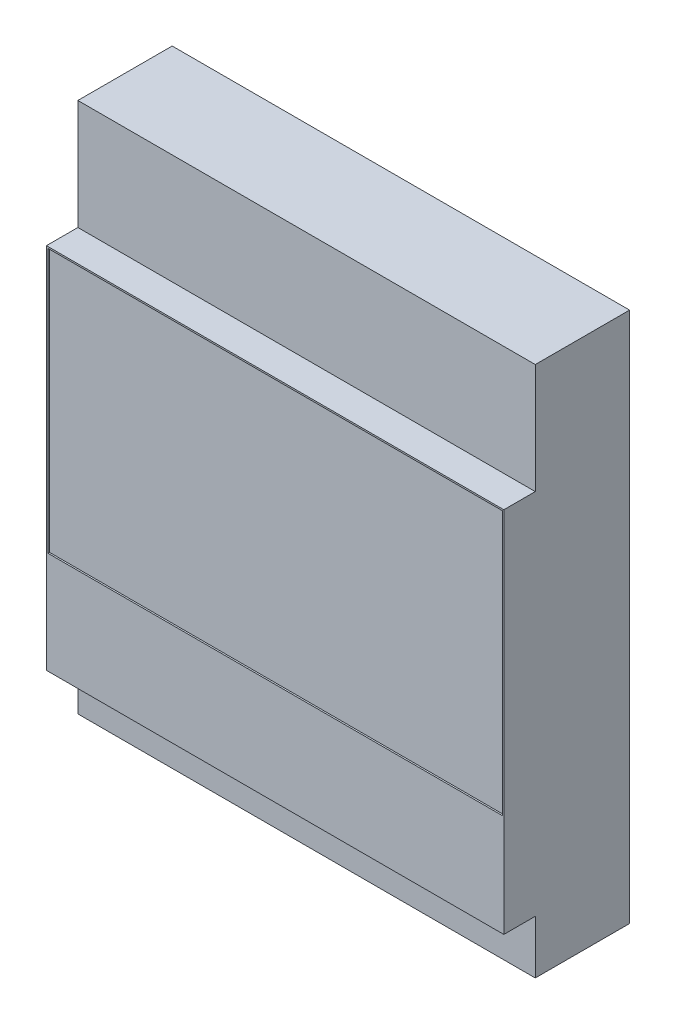
SolidWorks part; units mm, degrees
ref_plane "Спереди" through (0, 0, 0) normal (0, 0, 1) x (1, 0, 0)
ref_plane "Сверху" through (0, 0, 0) normal (0, 1, 0) x (1, 0, 0)
ref_plane "Справа" through (0, 0, 0) normal (1, 0, 0) x (0, 0, -1)
sketch "Эскиз1" plane through (0, 0, 0) normal (0, 0, 1) x (1, 0, 0)
  line L1 (-7.275, -5.85) -> (7.275, -5.85)
  line L2 (-7.275, -5.85) -> (-7.275, 5.85)
  line L3 (-7.275, 5.85) -> (7.275, 5.85)
  line L4 (7.275, -5.85) -> (7.275, 5.85)
  line L5 (-7.275, -5.85) -> (7.275, 5.85) construction
  line L6 (-7.275, 5.85) -> (7.275, -5.85) construction
  point P0 (0, 0)
  dimension "D1" = 14.55
  dimension "D2" = 11.7
extrude "Бобышка-Вытянуть1" add sketch "Эскиз1" along normal blind 1
sketch "Эскиз2" plane through (0, 0, 1) normal (0, 0, 1) x (1, 0, 0)
  line L0 (7.275, 5.85) -> (-7.275, 5.85) construction
  line L1 (-7.225, 5.8) -> (7.225, 5.8)
  line L2 (-7.225, 5.8) -> (-7.225, -2.6)
  line L3 (-7.225, -2.6) -> (7.225, -2.6)
  line L4 (7.225, 5.8) -> (7.225, -2.6)
  line L5 (7.275, -5.85) -> (7.275, 5.85) construction
  line L6 (-7.275, 5.85) -> (-7.275, -5.85) construction
  dimension "D1" = 0.05
  dimension "D2" = 0.05
  dimension "D3" = 0.05
  dimension "D4" = 8.45
extrude "Вырез-Вытянуть1" cut sketch "Эскиз2" against normal blind 0.05
sketch "Эскиз3" plane through (0, 0, 0) normal (0, 0, -1) x (-1, 0, 0)
  line L0 (7.275, 5.85) -> (7.275, -5.85) construction
  line L1 (-7.275, 9.35) -> (7.275, 9.35)
  line L2 (-7.275, 9.35) -> (-7.275, -7.55)
  line L3 (-7.275, -7.55) -> (7.275, -7.55)
  line L4 (7.275, 9.35) -> (7.275, -7.55)
  line L5 (-7.275, -5.85) -> (-7.275, 5.85) construction
  line L6 (7.275, -5.85) -> (-7.275, -5.85) construction
  line L7 (-7.275, 5.85) -> (7.275, 5.85) construction
  point P4 (0, 0)
  point P5 (7.9079, -7.6081)
  point P8 (0, 0)
  point P11 (0, 0)
  dimension "D1" = 1.7
  dimension "D2" = 3.5
extrude "Бобышка-Вытянуть2" add sketch "Эскиз3" along normal blind 3
